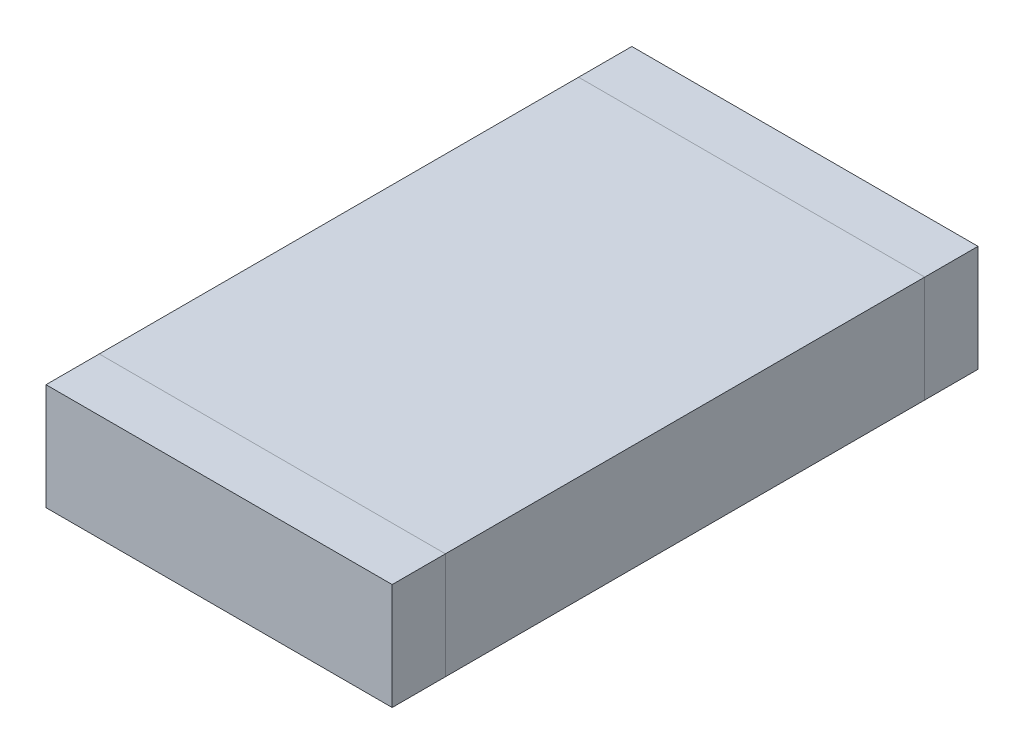
SolidWorks part; units mm, degrees
ref_plane "Front Plane" through (0, 0, 0) normal (0, 0, 1) x (1, 0, 0)
ref_plane "Top Plane" through (0, 0, 0) normal (0, 1, 0) x (1, 0, 0)
ref_plane "Right Plane" through (0, 0, 0) normal (1, 0, 0) x (0, 0, -1)
sketch "Sketch1" plane through (0, 0, 0) normal (0, 1, 0) x (1, 0, 0)
  line L1 (-0.65, 0.9) -> (0.65, 0.9)
  line L2 (-0.65, 0.9) -> (-0.65, -0.9)
  line L3 (-0.65, -0.9) -> (0.65, -0.9)
  line L4 (0.65, 0.9) -> (0.65, -0.9)
  line L5 (-0.65, 0.9) -> (0.65, -0.9) construction
  line L6 (-0.65, -0.9) -> (0.65, 0.9) construction
  point P0 (0, 0)
  dimension "Length" = 1.8
  dimension "Width" = 1.3
extrude "MB" add sketch "Sketch1" along normal blind 0.4
sketch "Sketch2" plane through (0, 0, 0.9) normal (0, 0, 1) x (1, 0, 0)
  line L4 (-0.65, 0) -> (0.65, 0)
  line L5 (0.65, 0) -> (0.65, 0.4)
  line L6 (0.65, 0.4) -> (-0.65, 0.4)
  line L7 (-0.65, 0.4) -> (-0.65, 0)
  line L8 (-0.65, 0) -> (0.65, 0)
  line L9 (0.65, 0) -> (0.65, 0.4)
  line L10 (0.65, 0.4) -> (-0.65, 0.4)
  line L11 (-0.65, 0.4) -> (-0.65, 0)
  dimension "D1" = 0
extrude "SB L" add sketch "Sketch2" along normal blind 0.2 separate body
sketch "Sketch3" plane through (0, 0, -0.9) normal (0, 0, -1) x (-1, 0, 0)
  line L4 (-0.65, 0) -> (0.65, 0)
  line L5 (0.65, 0) -> (0.65, 0.4)
  line L6 (0.65, 0.4) -> (-0.65, 0.4)
  line L7 (-0.65, 0.4) -> (-0.65, 0)
  line L8 (-0.65, 0) -> (0.65, 0)
  line L9 (0.65, 0) -> (0.65, 0.4)
  line L10 (0.65, 0.4) -> (-0.65, 0.4)
  line L11 (-0.65, 0.4) -> (-0.65, 0)
  dimension "D1" = 0
extrude "SB R" add sketch "Sketch3" along normal blind 0.2 separate body
